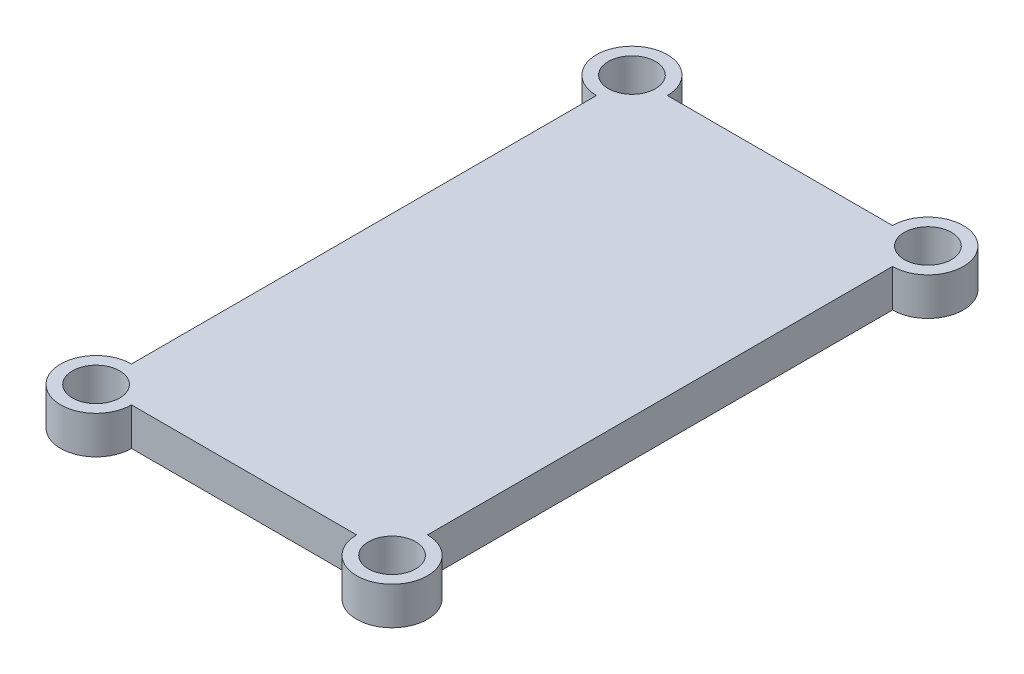
SolidWorks part; units mm, degrees
ref_plane "Front Plane" through (0, 0, 0) normal (0, 0, 1) x (1, 0, 0)
ref_plane "Top Plane" through (0, 0, 0) normal (0, 1, 0) x (1, 0, 0)
ref_plane "Right Plane" through (0, 0, 0) normal (1, 0, 0) x (0, 0, -1)
sketch "Sketch1" plane through (0, 1641.9879, 0) normal (0, 1, 0) x (1, 0, 0)
  line L1 (543.2678, -1480.076) -> (605.9678, -1480.076)
  line L2 (543.2678, -1480.076) -> (543.2678, -1366.576)
  line L3 (543.2678, -1366.576) -> (605.9678, -1366.576)
  line L4 (605.9678, -1480.076) -> (605.9678, -1366.576)
extrude "Boss-Extrude1" add sketch "Sketch1" along normal blind 8
sketch "Sketch2" plane through (0, 1641.9879, 0) normal (0, -1, 0) x (1, 0, 0)
  circle A0 centre (543.2678, 1366.576) radius 7.5
  circle A1 centre (605.9678, 1366.576) radius 7.5
  circle A2 centre (605.9678, 1480.076) radius 7.5
  circle A3 centre (543.2678, 1480.076) radius 7.5
  dimension "D1" = 15
extrude "Boss-Extrude2" add sketch "Sketch2" against normal blind 8
sketch "Sketch3" plane through (0, 1641.9879, 0) normal (0, -1, 0) x (1, 0, 0)
  circle A0 centre (543.2678, 1480.076) radius 5
  circle A1 centre (605.9678, 1480.076) radius 5
  circle A2 centre (605.9678, 1366.576) radius 5
  circle A3 centre (543.2678, 1366.576) radius 5
  dimension "D1" = 10
extrude "Cut-Extrude1" cut sketch "Sketch3" against normal blind 8
